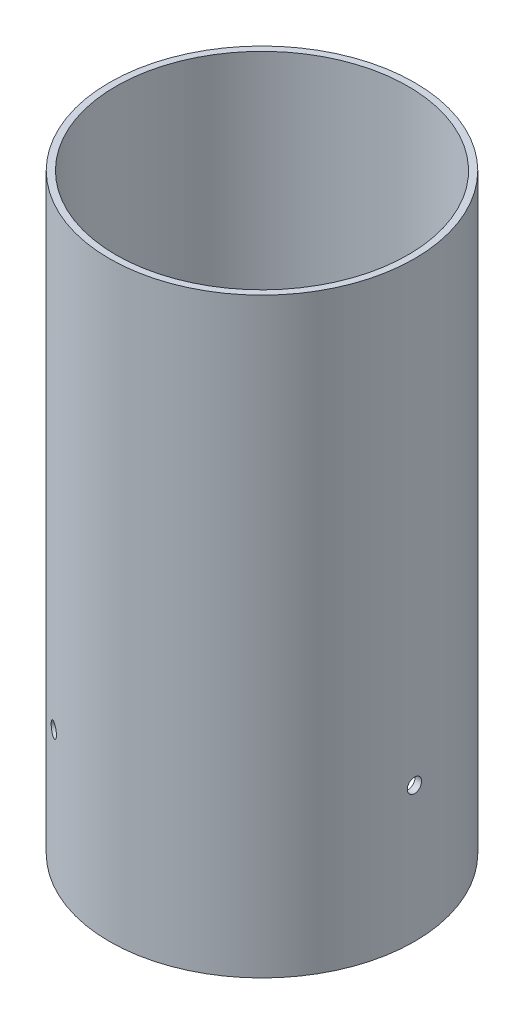
SolidWorks part; units mm, degrees
material "G12 Fiberglass"
ref_plane "Front Plane" through (0, 0, 0) normal (0, 0, 1) x (1, 0, 0)
ref_plane "Top Plane" through (0, 0, 0) normal (0, 1, 0) x (1, 0, 0)
ref_plane "Right Plane" through (0, 0, 0) normal (1, 0, 0) x (0, 0, -1)
sketch "Sketch1" plane through (0, 0, 0) normal (0, 1, 0) x (1, 0, 0)
  circle A0 centre (0, 0) radius 36.5125
  circle A1 centre (0, 0) radius 38.1381
  dimension "D1" = 73.025
  dimension "D2" = 1.6256
extrude "Boss-Extrude1" add sketch "Sketch1" along normal blind 147.8153
ref_axis "Axis1" through (0, 155.0861, 0) along (0, -1, 0)
ref_plane "Plane1" through (38.1381, 0, 0) normal (1, 0, 0) x (0, 0, -1)
sketch "Sketch2" plane through (38.1381, 0, 0) normal (1, 0, 0) x (0, 0, -1)
  line L0 (0, 155.0861) -> (0, -7.3851) construction
  circle A0 centre (0, 33.8074) radius 1.7859
  dimension "D1" = 3.5719
  dimension "D2" = 33.8074
extrude "Cut-Extrude1" cut sketch "Sketch2" against normal up to next
pattern_circular "CirPattern1" count 3 over 360 about axis through (0, 155.0861, 0) along (0, -1, 0) of "Cut-Extrude1"
